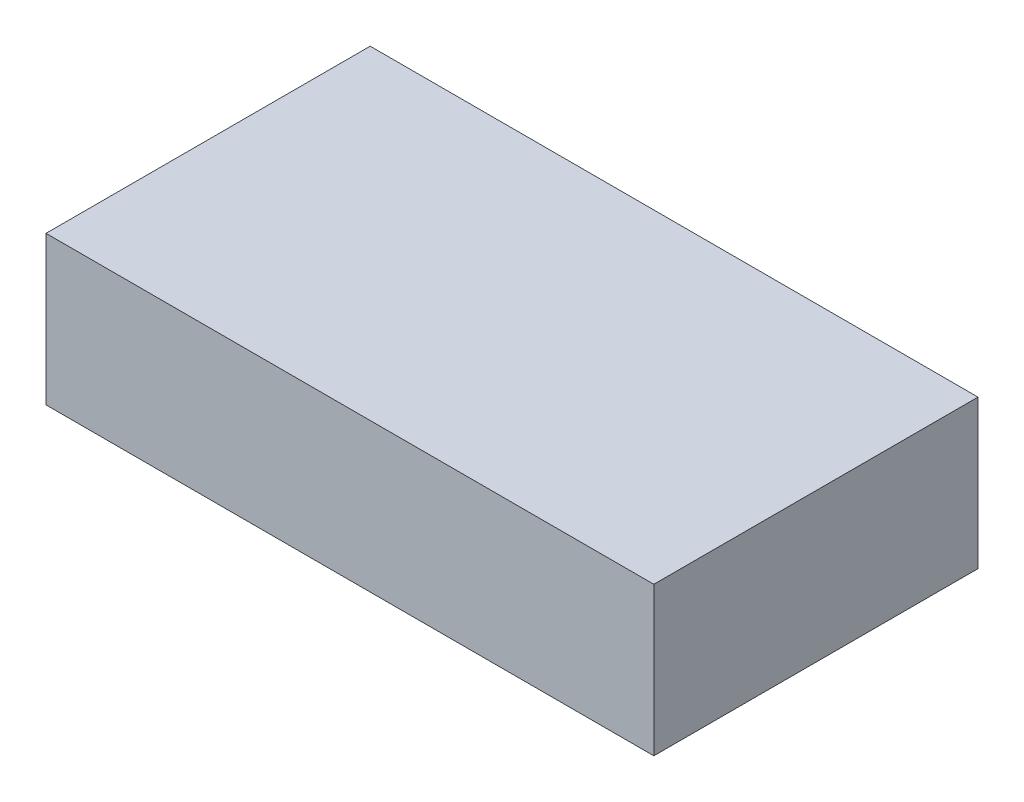
SolidWorks part; units mm, degrees
ref_plane "Front Plane" through (0, 0, 0) normal (0, 0, 1) x (1, 0, 0)
ref_plane "Top Plane" through (0, 0, 0) normal (0, 1, 0) x (1, 0, 0)
ref_plane "Right Plane" through (0, 0, 0) normal (1, 0, 0) x (0, 0, -1)
sketch "Sketch1" plane through (0, 0, 0) normal (0, 1, 0) x (1, 0, 0)
  line L1 (-22.5, -12) -> (22.5, -12)
  line L2 (-22.5, -12) -> (-22.5, 12)
  line L3 (-22.5, 12) -> (22.5, 12)
  line L4 (22.5, -12) -> (22.5, 12)
  line L5 (-22.5, -12) -> (22.5, 12) construction
  line L6 (-22.5, 12) -> (22.5, -12) construction
  point P0 (0, 0)
  dimension "D1" = 45
  dimension "D2" = 24
extrude "Boss-Extrude1" add sketch "Sketch1" along normal blind 11
